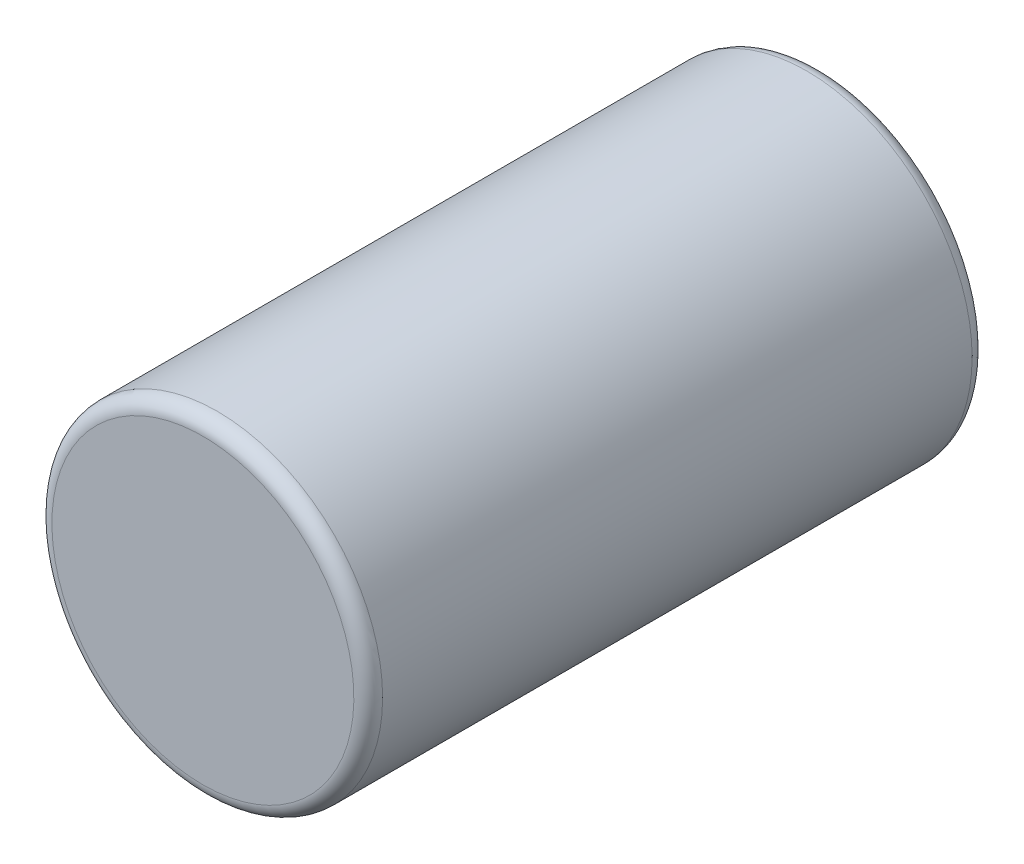
SolidWorks part; units mm, degrees
material "Verzinkter Stahl"
ref_plane "Ebene vorne" through (0, 0, 0) normal (0, 0, 1) x (1, 0, 0)
ref_plane "Ebene oben" through (0, 0, 0) normal (0, 1, 0) x (1, 0, 0)
ref_plane "Ebene rechts" through (0, 0, 0) normal (1, 0, 0) x (0, 0, -1)
sketch "Skizze1" plane through (0, 0, 0) normal (1, 0, 0) x (0, 0, -1)
  line L0 (0, 0) -> (0, 10.5)
  line L1 (1, 11.5) -> (42, 11.5)
  line L2 (43, 10.5) -> (43, 8)
  line L3 (43, 0) -> (0, 0)
  line L4 (0, 0) -> (52.2711, 0) construction
  line L5 (43, 8) -> (42.5, 7.5)
  line L6 (42.5, 7.5) -> (42.5, 5)
  line L7 (42.5, 5) -> (43, 4.5)
  line L8 (43, 4.5) -> (43, 0)
  arc A0 (42, 11.5) -> (43, 10.5) centre (42, 10.5) cw
  arc A1 (0, 10.5) -> (1, 11.5) centre (1, 10.5) cw
  dimension "D3" = 1
  dimension "D1" = 43
  dimension "D2" = 11.5
  dimension "D4" = 45
  dimension "D5" = 0.5
  dimension "D6" = 2.5
  dimension "D7" = 4.5
revolve "Rotation1" add sketch "Skizze1" angle 360 about L4
